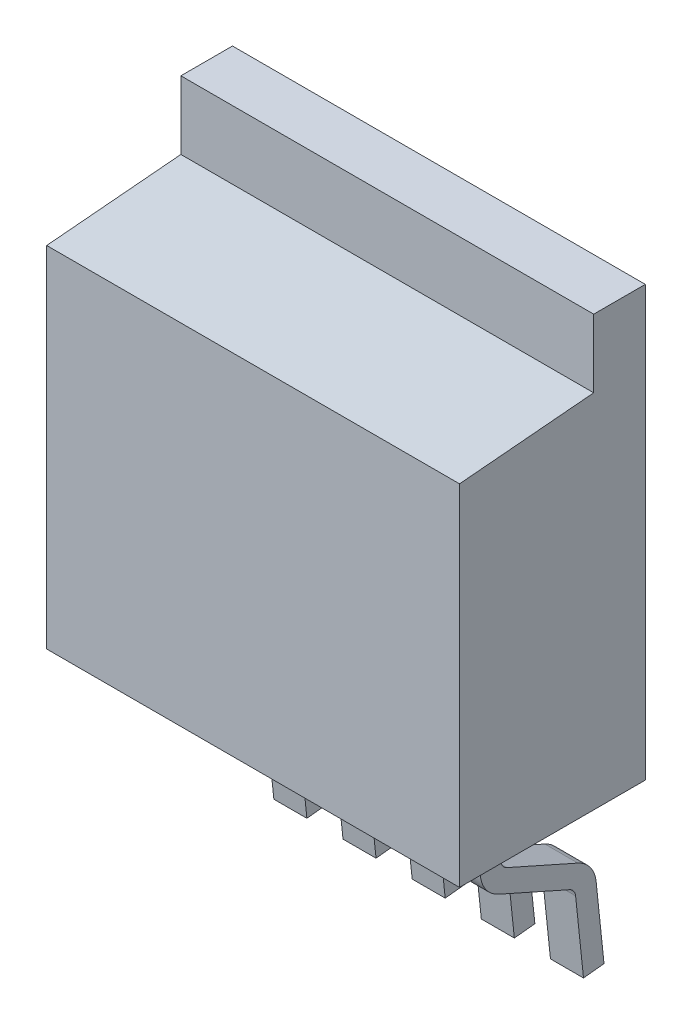
SolidWorks part; units mm, degrees
ref_plane "Front Plane" through (0, 0, 0) normal (0, 0, 1) x (1, 0, 0)
ref_plane "Top Plane" through (0, 0, 0) normal (0, 1, 0) x (1, 0, 0)
ref_plane "Right Plane" through (0, 0, 0) normal (1, 0, 0) x (0, 0, -1)
sketch "Sketch1" plane through (0, 0, 0) normal (0, 0, 1) x (1, 0, 0)
  line L1 (0, 0) -> (10.16, 0)
  line L2 (0, 0) -> (0, 10.5664)
  line L3 (0, 10.5664) -> (10.16, 10.5664)
  line L4 (10.16, 0) -> (10.16, 10.5664)
  dimension "D1" = 10.5664
  dimension "D2" = 10.16
extrude "Boss-Extrude1" add sketch "Sketch1" along normal blind 1.27
sketch "Sketch2" plane through (0, 0, 1.27) normal (0, 0, 1) x (1, 0, 0)
  line L0 (10.16, 0) -> (10.16, 10.5664) construction
  line L1 (0, 0) -> (10.16, 0)
  line L2 (0, 0) -> (0, 8.89)
  line L3 (0, 8.89) -> (10.16, 8.89)
  line L4 (10.16, 0) -> (10.16, 8.89)
  dimension "D1" = 8.89
extrude "Boss-Extrude2" add sketch "Sketch2" along normal blind 3.302
draft "Draft1" type of draft neutral plane draft angle 5 faces to draft 1 face at (6.35, 8.89, 3.7465) neutral plane through (0, 0, 1.27) neutral plane normal (0, 0, 1) parameters "D1"=5
ref_plane "Plane1" through (1.6764, 0, 0) normal (-1, 0, 0) x (0, 0, 1)
sketch "Sketch3" plane through (1.6764, 0, 0) normal (-1, 0, 0) x (0, 0, 1)
  line L0 (2.286, 0) -> (2.286, -1.3648)
  line L1 (4.572, 0) -> (0, 0) construction
  line L2 (2.286, -1.3648) -> (-0.0137, -2.3876)
  line L3 (-0.0137, -2.3876) -> (-0.254, -4.6736)
  line L4 (1.27, 10.5664) -> (0, 10.5664) construction
  line L5 (0, 10.5664) -> (0, 0) construction
  dimension "D1" = 2.286
  dimension "D2" = 15.24
  dimension "D3" = 6
  dimension "D4" = 0.254
extrude "Extrude-Thin1" add sketch "Sketch3" against normal mid plane 0.8128 thin thin type one direction reverse wall 0.508
pattern_linear "LPattern1" count 5 spacing 1.7018 along (1, 0, 0) of "Extrude-Thin1"
